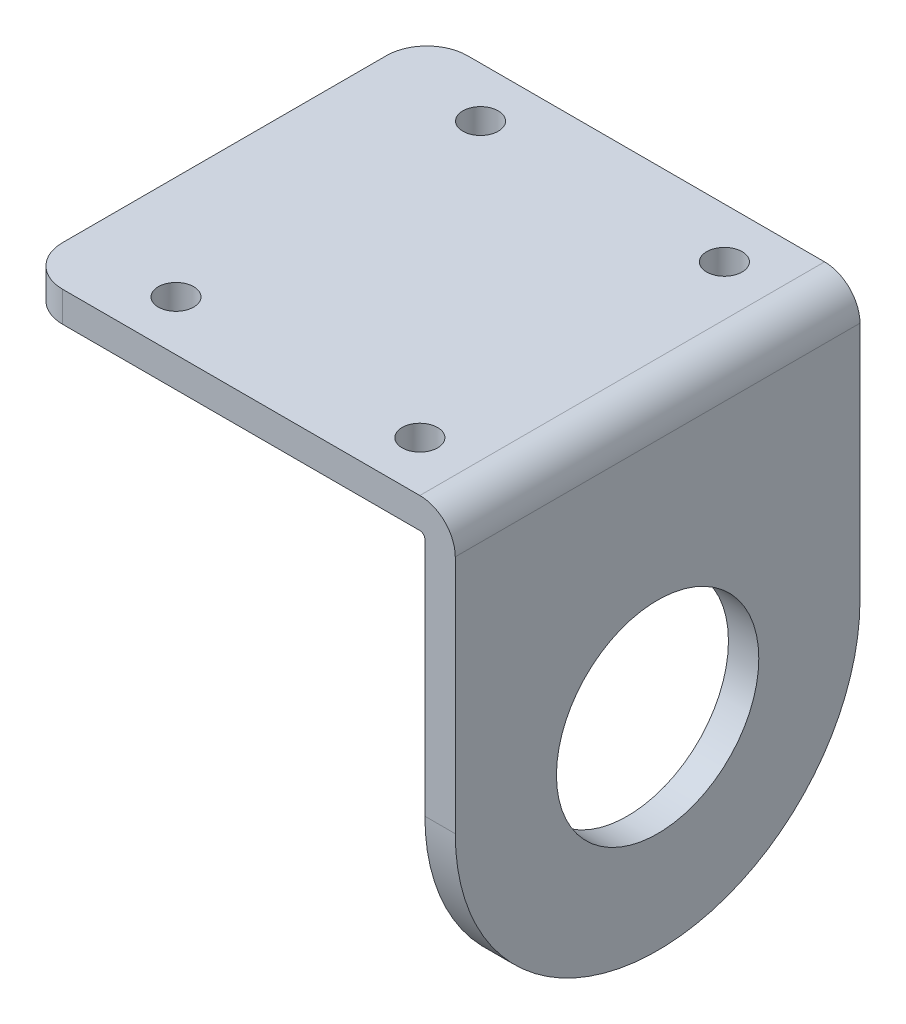
SolidWorks part; units mm, degrees
ref_plane "Front Plane" through (0, 0, 0) normal (0, 0, 1) x (1, 0, 0)
ref_plane "Top Plane" through (0, 0, 0) normal (0, 1, 0) x (1, 0, 0)
ref_plane "Right Plane" through (0, 0, 0) normal (1, 0, 0) x (0, 0, -1)
sketch "Sketch1" plane through (0, 0, 0) normal (1, 0, 0) x (0, 0, -1)
  line L0 (-20, 0) -> (-20, 27.2)
  line L1 (-20, 27.2) -> (20, 27.2)
  line L2 (20, 27.2) -> (20, 0)
  circle A0 centre (0, 0) radius 10
  circle A1 centre (0, 0) radius 20
  dimension "D1" = 20
  dimension "D2" = 40
  dimension "D3" = 47.2
extrude "Boss-Extrude1" add sketch "Sketch1" along normal blind 3 contours A1 L2 L1 L0 | A1 A0
sketch "Sketch2" plane through (3, 0, 0) normal (1, 0, 0) x (0, 0, -1)
  line L0 (20, 27.2) -> (20, 0) construction
  line L1 (-20, 27.2) -> (20, 27.2)
  line L2 (-20, 27.2) -> (-20, 24.2)
  line L3 (-20, 24.2) -> (20, 24.2)
  line L4 (20, 27.2) -> (20, 24.2)
  dimension "D1" = 3
extrude "Boss-Extrude2" add sketch "Sketch2" against normal blind 42.8
fillet "Fillet1" radius 0.5 1 edges at (0, 24.2, 0)
fillet "Fillet2" radius 3.5 1 edges at (3, 27.2, 0)
fillet "Fillet3" radius 4 2 edges at (-39.8, 25.7, 20) (-39.8, 25.7, -20)
sketch "Sketch3" plane through (0, 27.2, 0) normal (0, 1, 0) x (1, 0, 0)
  line L0 (-39.8, 15.05) -> (-0.5, 15.05) construction
  line L1 (-39.8, 16) -> (-39.8, -16) construction
  line L2 (-0.5, -20) -> (-0.5, 20) construction
  line L3 (-39.8, -15.05) -> (-0.5, -15.05) construction
  line L4 (-20.15, -15.05) -> (-20.15, 15.05) construction
  line L5 (-20.15, 0) -> (0, 0) construction
  line L6 (-0.5, -20) -> (-35.8, -20) construction
  line L7 (-29.55, -15.05) -> (-29.55, 15.05) construction
  line L8 (-5.45, 15.05) -> (-5.45, -15.05) construction
  circle A0 centre (-29.55, 15.05) radius 1.75
  circle A1 centre (-5.45, 15.05) radius 1.75
  circle A2 centre (-29.55, -15.05) radius 1.75
  circle A3 centre (-5.45, -15.05) radius 1.75
  dimension "D1" = 3.5
  dimension "D3" = 20.6
  dimension "D2" = 8.5
  dimension "D4" = 3.2
  dimension "D5" = 24.1
  dimension "D6" = 30.1
extrude "Cut-Extrude1" cut sketch "Sketch3" against normal blind 10
